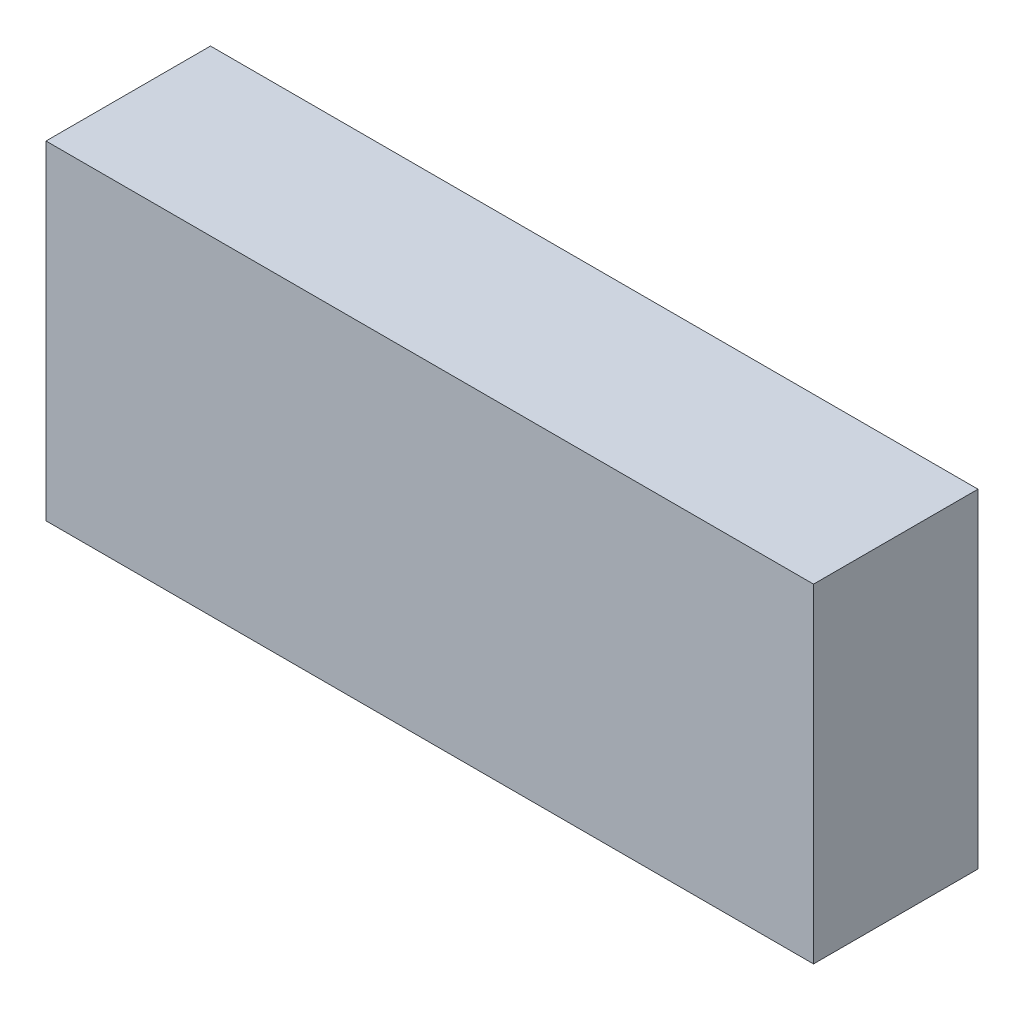
SolidWorks part; units mm, degrees
ref_plane "Front Plane" through (0, 0, 0) normal (0, 0, 1) x (1, 0, 0)
ref_plane "Top Plane" through (0, 0, 0) normal (0, 1, 0) x (1, 0, 0)
ref_plane "Right Plane" through (0, 0, 0) normal (1, 0, 0) x (0, 0, -1)
sketch "Sketch1" plane through (0, 0, 0) normal (0, 1, 0) x (1, 0, 0)
  line L1 (0, 0) -> (70, 0)
  line L2 (0, 0) -> (0, 15)
  line L3 (0, 15) -> (70, 15)
  line L4 (70, 0) -> (70, 15)
  dimension "D1" = 70
  dimension "D2" = 15
extrude "Boss-Extrude1" add sketch "Sketch1" along normal blind 30
